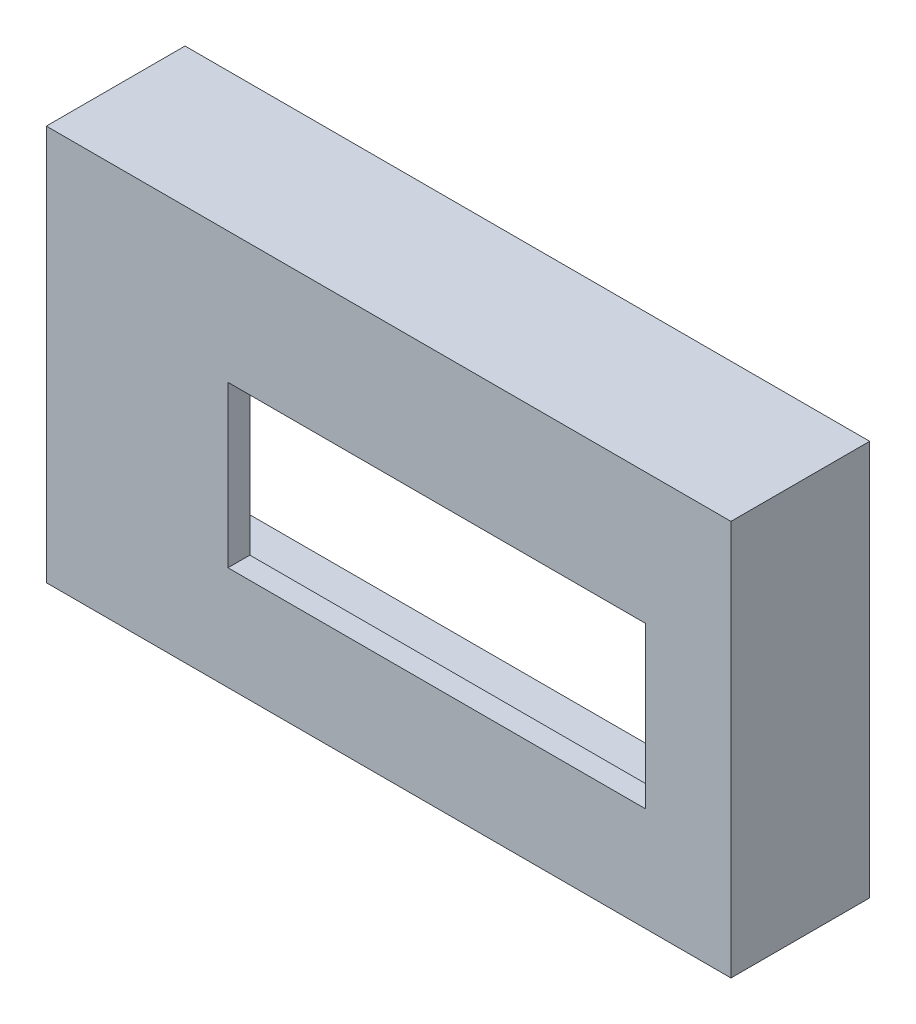
SolidWorks part; units mm, degrees
ref_plane "Front Plane" through (0, 0, 0) normal (0, 0, 1) x (1, 0, 0)
ref_plane "Top Plane" through (0, 0, 0) normal (0, 1, 0) x (1, 0, 0)
ref_plane "Right Plane" through (0, 0, 0) normal (1, 0, 0) x (0, 0, -1)
sketch "Sketch1" plane through (0, 0, 0) normal (0, 0, 1) x (1, 0, 0)
  line L1 (91.572, -14.4956) -> (-27.533, -14.4956)
  line L2 (91.572, -14.4956) -> (91.572, 54.3008)
  line L3 (91.572, 54.3008) -> (-27.533, 54.3008)
  line L4 (-27.533, -14.4956) -> (-27.533, 54.3008)
  line L14 (4.064, 31.496) -> (4.064, 3.556)
  line L15 (4.064, 3.556) -> (76.708, 3.556)
  line L16 (76.708, 31.496) -> (4.064, 31.496)
  line L17 (76.708, 3.556) -> (76.708, 31.496)
  line L18 (4.064, 31.496) -> (4.064, 3.556)
  line L19 (4.064, 3.556) -> (76.708, 3.556)
  line L20 (76.708, 31.496) -> (4.064, 31.496)
  line L21 (76.708, 3.556) -> (76.708, 31.496)
  dimension "D1" = 0.508
extrude "Boss-Extrude2" add sketch "Sketch1" along normal blind 3.81
sketch "Sketch2" plane through (0, 0, 0) normal (0, 0, 1) x (1, 0, 0)
  line L0 (-23.723, 50.4908) -> (-23.723, -10.6856)
  line L1 (-27.533, 54.3008) -> (91.572, 54.3008)
  line L2 (-27.533, 54.3008) -> (-27.533, -14.4956)
  line L3 (-27.533, -14.4956) -> (91.572, -14.4956)
  line L4 (91.572, 54.3008) -> (91.572, -14.4956)
  line L5 (-23.723, -10.6856) -> (87.762, -10.6856)
  line L6 (87.762, 50.4908) -> (87.762, -10.6856)
  line L7 (-23.723, 50.4908) -> (87.762, 50.4908)
  dimension "D1" = 3.81
extrude "Boss-Extrude3" add sketch "Sketch2" against normal blind 20.32
